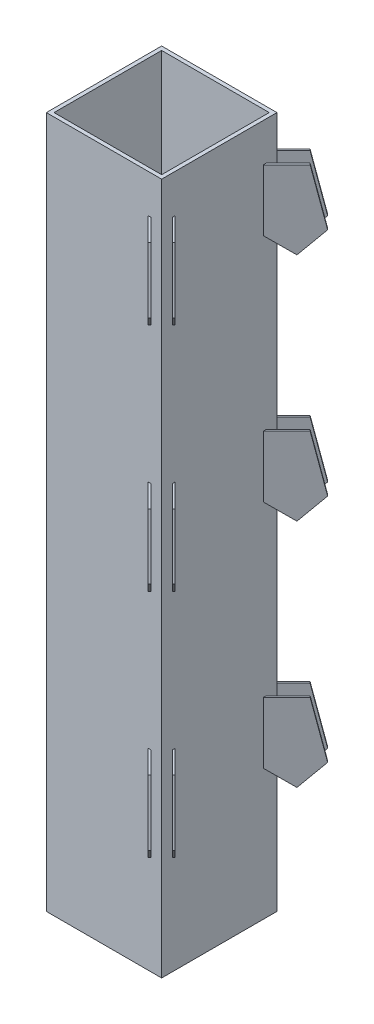
SolidWorks part; units mm, degrees
ref_plane "Front Plane" through (0, 0, 0) normal (0, 0, 1) x (1, 0, 0)
ref_plane "Top Plane" through (0, 0, 0) normal (0, 1, 0) x (1, 0, 0)
ref_plane "Right Plane" through (0, 0, 0) normal (1, 0, 0) x (0, 0, -1)
sketch "Sketch1" plane through (0, 0, 0) normal (1, 0, 0) x (0, 0, -1)
  line L1 (0, 0) -> (-3000, 0)
  line L2 (0, 0) -> (0, 18000)
  line L3 (0, 18000) -> (-3000, 18000)
  line L4 (-3000, 0) -> (-3000, 18000)
  dimension "D1" = 18000
  dimension "D2" = 3000
extrude "Boss-Extrude1" add sketch "Sketch1" along normal blind 3000
sketch "Sketch2" plane through (0, 0, 0) normal (0, -1, 0) x (1, 0, 0)
  line L0 (3000, 3000) -> (3000, 0) construction
  line L1 (3000, 0) -> (7012.4924, -4012.4924) construction
  dimension "D1" = 45
  dimension "D2" = 135
ref_plane "Mid Plane1" through (1500, 0, 1500) normal (-0.7071, 0, -0.7071) x (0, 1, 0)
ref_plane "Plane2" through (1358.5786, 0, 1358.5786) normal (-0.7071, 0, -0.7071) x (0, 1, 0)
ref_plane "Plane3" through (1641.4214, 0, 1641.4214) normal (-0.7071, 0, -0.7071) x (0, 1, 0)
sketch "Sketch3" plane through (1358.5786, 0, 1358.5786) normal (-0.7071, 0, -0.7071) x (0, 1, 0)
  line L0 (17000, 1731.3203) -> (17000, 2731.3203)
  line L1 (17000, 2731.3203) -> (15535.2415, 3054.5581)
  line L2 (15535.2415, 3054.5581) -> (14969.5561, 2488.8727)
  line L3 (14969.5561, 2488.8727) -> (15500, 1731.3203)
  line L4 (15500, 1731.3203) -> (17000, 1731.3203)
  line L5 (11000, 1731.3203) -> (11000, 2731.3203)
  line L6 (11000, 2731.3203) -> (9535.2415, 3054.5581)
  line L7 (9535.2415, 3054.5581) -> (8969.5561, 2488.8727)
  line L8 (8969.5561, 2488.8727) -> (9500, 1731.3203)
  line L9 (9500, 1731.3203) -> (11000, 1731.3203)
  line L10 (5000, 1731.3203) -> (5000, 2731.3203)
  line L11 (5000, 2731.3203) -> (3535.2415, 3054.5581)
  line L12 (3535.2415, 3054.5581) -> (2969.5561, 2488.8727)
  line L13 (2969.5561, 2488.8727) -> (3500, 1731.3203)
  line L14 (3500, 1731.3203) -> (5000, 1731.3203)
  line L15 (15500, 1731.3203) -> (11000, 1731.3203) construction
  line L16 (9500, 1731.3203) -> (5000, 1731.3203) construction
  line L17 (0, 2121.3203) -> (18000, 2121.3203) construction
  dimension "D1" = 45
  dimension "D2" = 1000
  dimension "D3" = 800
  dimension "D4" = 100
  dimension "D5" = 1500
  dimension "D6" = 45
  dimension "D7" = 1000
  dimension "D8" = 800
  dimension "D9" = 100
  dimension "D10" = 1500
  dimension "D11" = 45
  dimension "D12" = 1000
  dimension "D13" = 800
  dimension "D14" = 100
  dimension "D15" = 1500
  dimension "D16" = 1500
  dimension "D17" = 1500
  dimension "D18" = 1500
  dimension "D19" = 17000
  dimension "D20" = 390
  dimension "D21" = 4500
extrude "Boss-Extrude2" add sketch "Sketch3" along normal blind 50
sketch "Sketch4" plane through (1641.4214, 0, 1641.4214) normal (-0.7071, 0, -0.7071) x (0, 1, 0)
  line L0 (5000, 2731.3203) -> (5000, 1921.3203) construction
  line L2 (3366.9606, 1921.3203) -> (2969.5561, 2488.8727) construction
  line L3 (2969.5561, 2488.8727) -> (3535.2415, 3054.5581) construction
  line L4 (3535.2415, 3054.5581) -> (5000, 2731.3203) construction
  line L5 (11000, 2731.3203) -> (11000, 1921.3203) construction
  line L7 (9366.9606, 1921.3203) -> (8969.5561, 2488.8727) construction
  line L8 (8969.5561, 2488.8727) -> (9535.2415, 3054.5581) construction
  line L9 (9535.2415, 3054.5581) -> (11000, 2731.3203) construction
  line L10 (17000, 2731.3203) -> (17000, 1921.3203) construction
  line L12 (15366.9606, 1921.3203) -> (14969.5561, 2488.8727) construction
  line L13 (14969.5561, 2488.8727) -> (15535.2415, 3054.5581) construction
  line L14 (15535.2415, 3054.5581) -> (17000, 2731.3203) construction
  line L15 (5000, 2731.3203) -> (5000, 1871.3203)
  line L17 (3401.9709, 1871.3203) -> (2969.5561, 2488.8727)
  line L18 (2969.5561, 2488.8727) -> (3535.2415, 3054.5581)
  line L19 (3535.2415, 3054.5581) -> (5000, 2731.3203)
  line L20 (11000, 2731.3203) -> (11000, 1871.3203)
  line L22 (9401.9709, 1871.3203) -> (8969.5561, 2488.8727)
  line L23 (8969.5561, 2488.8727) -> (9535.2415, 3054.5581)
  line L24 (9535.2415, 3054.5581) -> (11000, 2731.3203)
  line L25 (17000, 2731.3203) -> (17000, 1871.3203)
  line L27 (15401.9709, 1871.3203) -> (14969.5561, 2488.8727)
  line L28 (14969.5561, 2488.8727) -> (15535.2415, 3054.5581)
  line L29 (15535.2415, 3054.5581) -> (17000, 2731.3203)
  line L30 (11000, 1871.3203) -> (9401.9709, 1871.3203) construction
  line L34 (17000, 1871.3203) -> (15401.9709, 1871.3203) construction
  line L35 (5000, 1871.3203) -> (3401.9709, 1871.3203) construction
  line L36 (17000, 1871.3203) -> (15401.9709, 1871.3203)
  line L37 (11000, 1871.3203) -> (9401.9709, 1871.3203)
  line L38 (5000, 1871.3203) -> (3401.9709, 1871.3203)
  line L39 (15401.9709, 1871.3203) -> (11000, 1871.3203) construction
  line L40 (5000, 1871.3203) -> (9401.9709, 1871.3203) construction
extrude "Boss-Extrude3" add sketch "Sketch4" against normal blind 50 separate body
sketch "Sketch5" plane through (0, 18000, 0) normal (0, 1, 0) x (1, 0, 0)
  line L0 (1500, 0) -> (1500, -3000) construction
  line L1 (100, -100) -> (2900, -100)
  line L2 (100, -100) -> (100, -2900)
  line L3 (100, -2900) -> (2900, -2900)
  line L4 (2900, -100) -> (2900, -2900)
  line L5 (100, -100) -> (2900, -2900) construction
  line L6 (100, -2900) -> (2900, -100) construction
  line L7 (3000, 0) -> (0, 0) construction
  line L9 (3000, -3000) -> (0, -3000) construction
  line L10 (3000, -3000) -> (3000, 0) construction
  point P0 (1500, -1500)
  point P14 (1500, -1500)
  dimension "D1" = 100
  dimension "D2" = 100
extrude "Cut-Extrude1" cut sketch "Sketch5" against normal blind 18305
ref_plane "Mid Plane4" through (0, 0, 0) normal (-0.7071, 0, 0.7071) x (0, -1, 0)
ref_plane "Plane5" through (-141.4214, 0, 141.4214) normal (-0.7071, 0, 0.7071) x (0, -1, 0)
ref_plane "Plane6" through (141.4214, 0, -141.4214) normal (-0.7071, 0, 0.7071) x (0, -1, 0)
sketch "Sketch8" plane through (-141.4214, 0, 141.4214) normal (-0.7071, 0, 0.7071) x (0, -1, 0)
  line L15 (-17000, 3852.6407) -> (-17000, 2371.3203) construction
  line L16 (-18000, 4242.6407) -> (0, 4242.6407) construction
  line L17 (-14969.5561, 4610.1931) -> (-2969.5576, 4610.1931) construction
  line L18 (-9500, 3852.6407) -> (-5000, 3852.6407) construction
  line L19 (-15500, 3852.6407) -> (-11000, 3852.6407) construction
  line L20 (-3500, 3852.6407) -> (-5000, 3852.6407)
  line L21 (-2969.5576, 4610.1931) -> (-3500, 3852.6407)
  line L22 (-3535.2415, 5175.8785) -> (-2969.5576, 4610.1931)
  line L23 (-5000, 4852.6407) -> (-3535.2415, 5175.8785)
  line L24 (-5000, 3852.6407) -> (-5000, 4852.6407)
  line L25 (-9500, 3852.6407) -> (-11000, 3852.6407)
  line L26 (-8969.5576, 4610.1931) -> (-9500, 3852.6407)
  line L27 (-9535.2415, 5175.8785) -> (-8969.5576, 4610.1931)
  line L28 (-11000, 4852.6407) -> (-9535.2415, 5175.8785)
  line L29 (-11000, 3852.6407) -> (-11000, 4852.6407)
  line L30 (-15500, 3852.6407) -> (-17000, 3852.6407)
  line L31 (-14969.5561, 4610.1931) -> (-15500, 3852.6407)
  line L32 (-15535.2415, 5175.8785) -> (-14969.5561, 4610.1931)
  line L33 (-17000, 4852.6407) -> (-15535.2415, 5175.8785)
  line L34 (-17000, 3852.6407) -> (-17000, 4852.6407)
  line L35 (-15535.2415, 5175.8785) -> (-3535.2415, 5175.8785) construction
  line L36 (-17000, 4852.6407) -> (-5000, 4852.6407) construction
  line L37 (0, 4242.6407) -> (0, 2121.3203) construction
  dimension "D1" = 1000
  dimension "D2" = 1500
  dimension "D3" = 800
  dimension "D4" = 100
  dimension "D5" = 1500
  dimension "D6" = 390
  dimension "D7" = 45
  dimension "D8" = 4500
  dimension "D9" = 17000
  dimension "D10" = 1500
  dimension "D11" = 1500
extrude "Boss-Extrude4" add sketch "Sketch8" along normal blind 50
sketch "Sketch9" plane through (141.4214, 0, -141.4214) normal (-0.7071, 0, 0.7071) x (0, -1, 0)
  line L0 (-5000, 3992.6407) -> (-3401.9712, 3992.6407) construction
  line L1 (-3401.9712, 3992.6407) -> (-2969.5576, 4610.1931) construction
  line L2 (-2969.5576, 4610.1931) -> (-3535.2415, 5175.8785) construction
  line L3 (-3535.2415, 5175.8785) -> (-5000, 4852.6407) construction
  line L4 (-5000, 4852.6407) -> (-5000, 3992.6407) construction
  line L5 (-11000, 3992.6407) -> (-9401.9712, 3992.6407) construction
  line L6 (-9401.9712, 3992.6407) -> (-8969.5576, 4610.1931) construction
  line L7 (-8969.5576, 4610.1931) -> (-9535.2415, 5175.8785) construction
  line L8 (-9535.2415, 5175.8785) -> (-11000, 4852.6407) construction
  line L9 (-11000, 4852.6407) -> (-11000, 3992.6407) construction
  line L10 (-17000, 3992.6407) -> (-15401.9709, 3992.6407) construction
  line L11 (-15401.9709, 3992.6407) -> (-14969.5561, 4610.1931) construction
  line L12 (-14969.5561, 4610.1931) -> (-15535.2415, 5175.8785) construction
  line L13 (-15535.2415, 5175.8785) -> (-17000, 4852.6407) construction
  line L14 (-17000, 4852.6407) -> (-17000, 3992.6407) construction
  line L15 (-5000, 3992.6407) -> (-3401.9712, 3992.6407)
  line L16 (-3401.9712, 3992.6407) -> (-2969.5576, 4610.1931)
  line L17 (-2969.5576, 4610.1931) -> (-3535.2415, 5175.8785)
  line L18 (-3535.2415, 5175.8785) -> (-5000, 4852.6407)
  line L19 (-5000, 4852.6407) -> (-5000, 3992.6407)
  line L20 (-11000, 3992.6407) -> (-9401.9712, 3992.6407)
  line L21 (-9401.9712, 3992.6407) -> (-8969.5576, 4610.1931)
  line L22 (-8969.5576, 4610.1931) -> (-9535.2415, 5175.8785)
  line L23 (-9535.2415, 5175.8785) -> (-11000, 4852.6407)
  line L24 (-11000, 4852.6407) -> (-11000, 3992.6407)
  line L25 (-17000, 3992.6407) -> (-15401.9709, 3992.6407)
  line L26 (-15401.9709, 3992.6407) -> (-14969.5561, 4610.1931)
  line L27 (-14969.5561, 4610.1931) -> (-15535.2415, 5175.8785)
  line L28 (-15535.2415, 5175.8785) -> (-17000, 4852.6407)
  line L29 (-17000, 4852.6407) -> (-17000, 3992.6407)
extrude "Boss-Extrude5" add sketch "Sketch9" against normal blind 50
